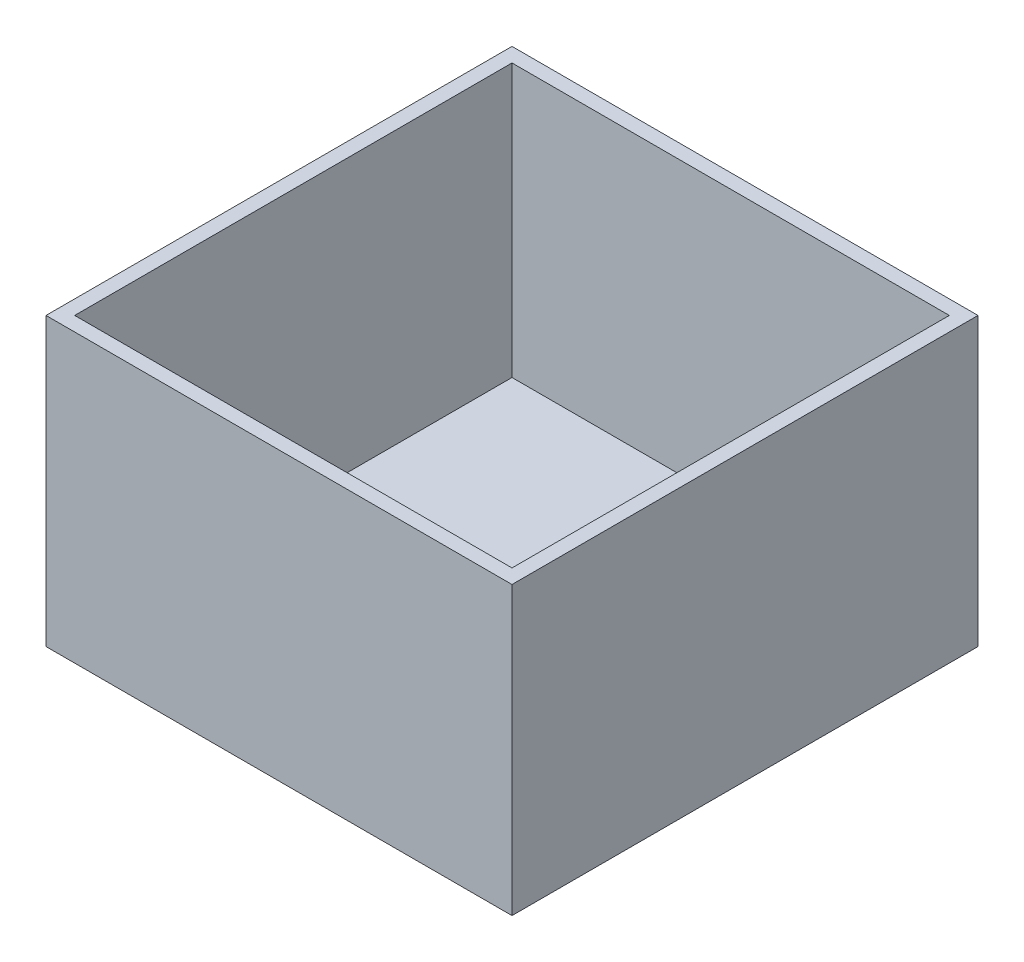
SolidWorks part; units mm, degrees
material "ABS"
ref_plane "Front Plane" through (0, 0, 0) normal (0, 0, 1) x (1, 0, 0)
ref_plane "Top Plane" through (0, 0, 0) normal (0, 1, 0) x (1, 0, 0)
ref_plane "Right Plane" through (0, 0, 0) normal (1, 0, 0) x (0, 0, -1)
sketch "Sketch1" plane through (0, 0, 0) normal (0, 1, 0) x (1, 0, 0)
  line L1 (0, 0) -> (82.55, 0)
  line L2 (0, 0) -> (0, -82.55)
  line L3 (0, -82.55) -> (82.55, -82.55)
  line L4 (82.55, 0) -> (82.55, -82.55)
extrude "Boss-Extrude1" add sketch "Sketch1" along normal blind 50.8
shell "Shell1" thickness 2.54
